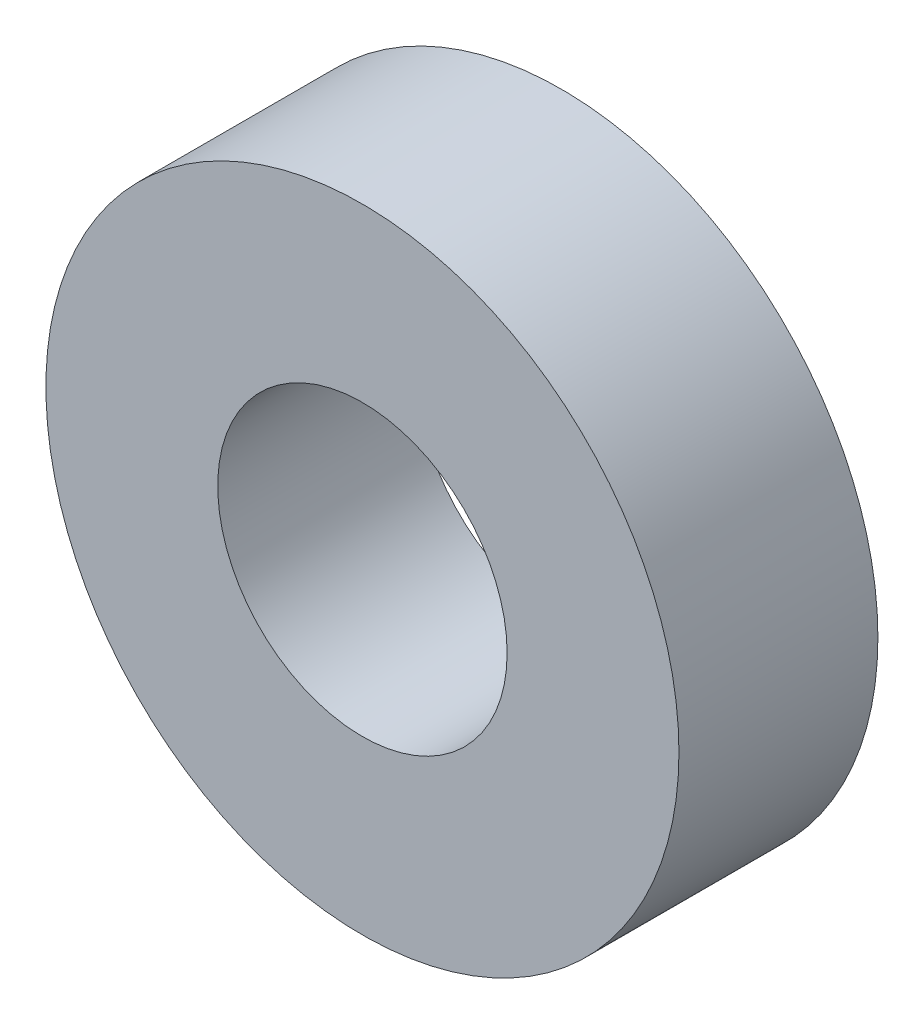
SolidWorks part; units mm, degrees
ref_plane "Front Plane" through (0, 0, 0) normal (0, 0, 1) x (1, 0, 0)
ref_plane "Top Plane" through (0, 0, 0) normal (0, 1, 0) x (1, 0, 0)
ref_plane "Right Plane" through (0, 0, 0) normal (1, 0, 0) x (0, 0, -1)
sketch "Sketch1" plane through (0, 0, 0) normal (0, 0, 1) x (1, 0, 0)
  circle A0 centre (0, 0) radius 8
  circle A1 centre (0, 0) radius 17.5
extrude "Boss-Extrude1" add sketch "Sketch1" along normal blind 11
